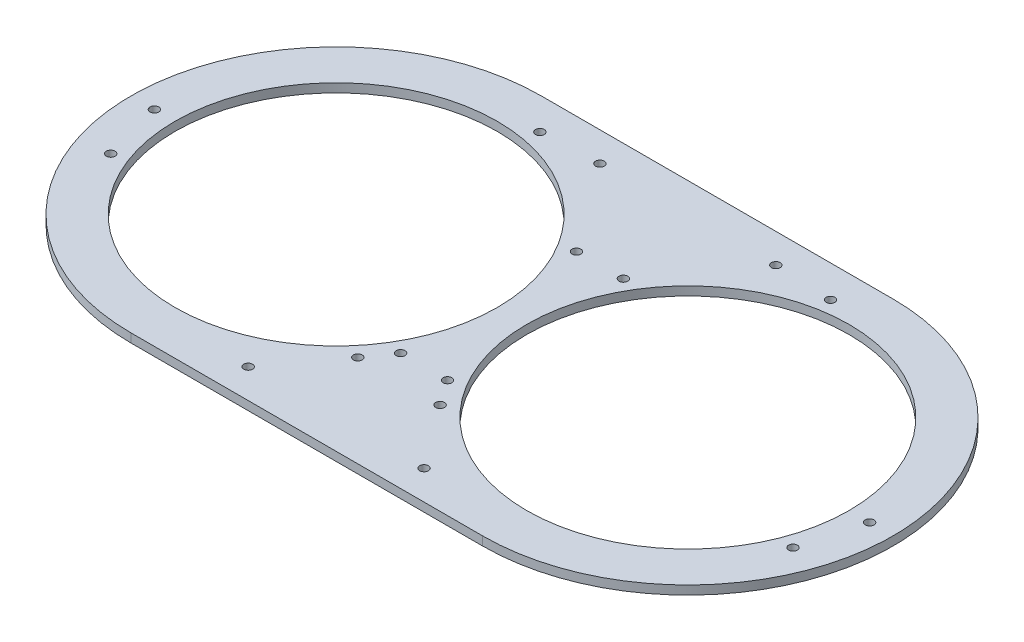
SolidWorks part; units mm, degrees
ref_plane "前视基准面" through (0, 0, 0) normal (0, 0, 1) x (1, 0, 0)
ref_plane "上视基准面" through (0, 0, 0) normal (0, 1, 0) x (1, 0, 0)
ref_plane "右视基准面" through (0, 0, 0) normal (1, 0, 0) x (0, 0, -1)
sketch "草图1" plane through (0, 0, 0) normal (0, 1, 0) x (1, 0, 0)
  line L0 (0, 0) -> (0, 89.0672) construction
  line L1 (-60, 0) -> (60, 0) construction
  line L2 (-60, 70) -> (60, 70)
  line L3 (-60, -70) -> (60, -70)
  line L4 (-90, 51.9615) -> (-60, 0) construction
  line L5 (-90, -51.9615) -> (-60, 0) construction
  line L6 (90, -51.9615) -> (60, 0) construction
  line L7 (90, 51.9615) -> (60, 0) construction
  line L8 (0, 0) -> (76.6344, 0) construction
  line L9 (-49.5811, 59.0885) -> (-60, 0) construction
  line L10 (-116.3816, -20.5212) -> (-60, 0) construction
  line L11 (-14.0373, -38.5673) -> (-60, 0) construction
  circle A0 centre (-60, 0) radius 55
  circle A1 centre (60, 0) radius 55
  arc A2 (-60, 70) -> (-60, -70) centre (-60, 0) ccw
  arc A3 (60, -70) -> (60, 70) centre (60, 0) ccw
  circle A4 centre (0, 0) radius 1.5 construction
  circle A5 centre (-90, 51.9615) radius 1.5 construction
  circle A6 centre (-90, -51.9615) radius 1.5 construction
  circle A7 centre (90, -51.9615) radius 1.5 construction
  circle A8 centre (90, 51.9615) radius 1.5 construction
  circle A9 centre (0, 0) radius 1.5 construction
  circle A10 centre (-122, 0) radius 1.5
  circle A11 centre (122, 0) radius 1.5
  circle A12 centre (-30, 60) radius 1.5
  circle A13 centre (30, 60) radius 1.5
  circle A14 centre (30, -60) radius 1.5
  circle A15 centre (-30, -60) radius 1.5
  circle A16 centre (-49.5811, 59.0885) radius 1.5
  circle A17 centre (-116.3816, -20.5212) radius 1.5
  circle A18 centre (-14.0373, -38.5673) radius 1.5
  circle A19 centre (14.0373, -38.5673) radius 1.5
  circle A20 centre (116.3816, -20.5212) radius 1.5
  circle A21 centre (49.5811, 59.0885) radius 1.5
  point P7 (0, 0)
  dimension "D1" = 110
  dimension "D2" = 60
  dimension "D3" = 15
  dimension "D4" = 3
  dimension "D5" = 60
  dimension "D6" = 60
  dimension "D7" = 3
  dimension "D9" = 3
  dimension "D10" = 60
  dimension "D12" = 3
  dimension "D13" = 62
  dimension "D14" = 62
  dimension "D15" = 3
  dimension "D16" = 3
  dimension "D18" = 60
  dimension "D19" = 3
  dimension "D22" = 3
  dimension "D23" = 60
  dimension "D25" = 3
  dimension "D8" = 120
  dimension "D11" = 120
  dimension "D17" = 30
  dimension "D20" = 60
  dimension "D21" = 80
  dimension "D24" = 120
  dimension "D26" = 60
  dimension "D27" = 120
extrude "凸台-拉伸2" add sketch "草图1" along normal blind 3 contours L3 A3 L2 A2 A13 A12 A11 A10 A7 A6 A5 A4 A1 A0 A8 A14 A15
sketch "草图2" plane through (0, 3, 0) normal (0, 1, 0) x (1, 0, 0)
  line L0 (0, 0) -> (15.6144, 0) construction
  line L1 (0, 0) -> (0, 23.8801) construction
  circle A0 centre (-8, -30) radius 1.5
  circle A1 centre (8, -30) radius 1.5
  circle A2 centre (8, 30) radius 1.5
  circle A3 centre (-8, 30) radius 1.5
  dimension "D1" = 3
  dimension "D2" = 30
  dimension "D3" = 8
extrude "切除-拉伸1" cut sketch "草图2" against normal blind 10
